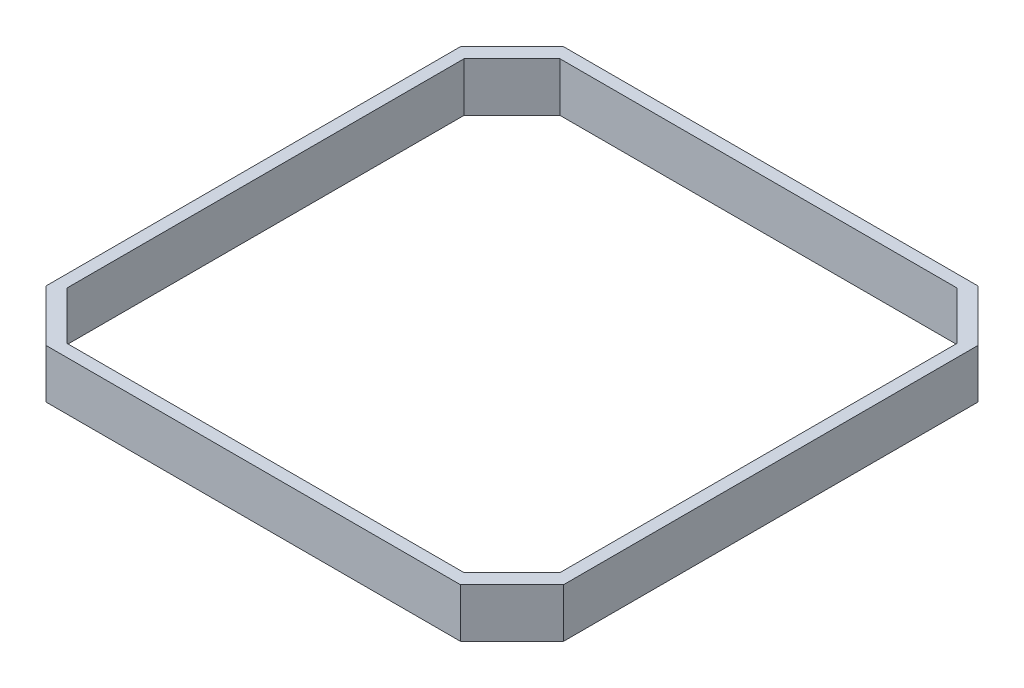
SolidWorks part; units mm, degrees
ref_plane "前视基准面" through (0, 0, 0) normal (0, 0, 1) x (1, 0, 0)
ref_plane "上视基准面" through (0, 0, 0) normal (0, 1, 0) x (1, 0, 0)
ref_plane "右视基准面" through (0, 0, 0) normal (1, 0, 0) x (0, 0, -1)
other "Configuration Table"
sketch "草图1" plane through (0, 0, 0) normal (0, 1, 0) x (1, 0, 0)
  line L0 (-1, -1) -> (-1, 41.2)
  line L1 (0, 0) -> (40.2, 0)
  line L2 (0, 0) -> (0, 40.2)
  line L3 (0, 40.2) -> (40.2, 40.2)
  line L4 (40.2, 0) -> (40.2, 40.2)
  line L5 (-1, 41.2) -> (41.2, 41.2)
  line L6 (41.2, -1) -> (41.2, 41.2)
  line L7 (-1, -1) -> (41.2, -1)
  dimension "D1" = 40.2
  dimension "D2" = 40.2
  dimension "D3" = 1
extrude "凸台-拉伸1" add sketch "草图1" along normal blind 4
chamfer "倒角1" distance 3.9 angle 45 4 edges at (40.2, 2, 0) (0, 2, 0) (40.2, 2, -40.2) (0, 2, -40.2)
chamfer "倒角2" distance 4.2 angle 45 4 edges at (-1, 2, 1) (41.2, 2, 1) (41.2, 2, -41.2) (-1, 2, -41.2)
